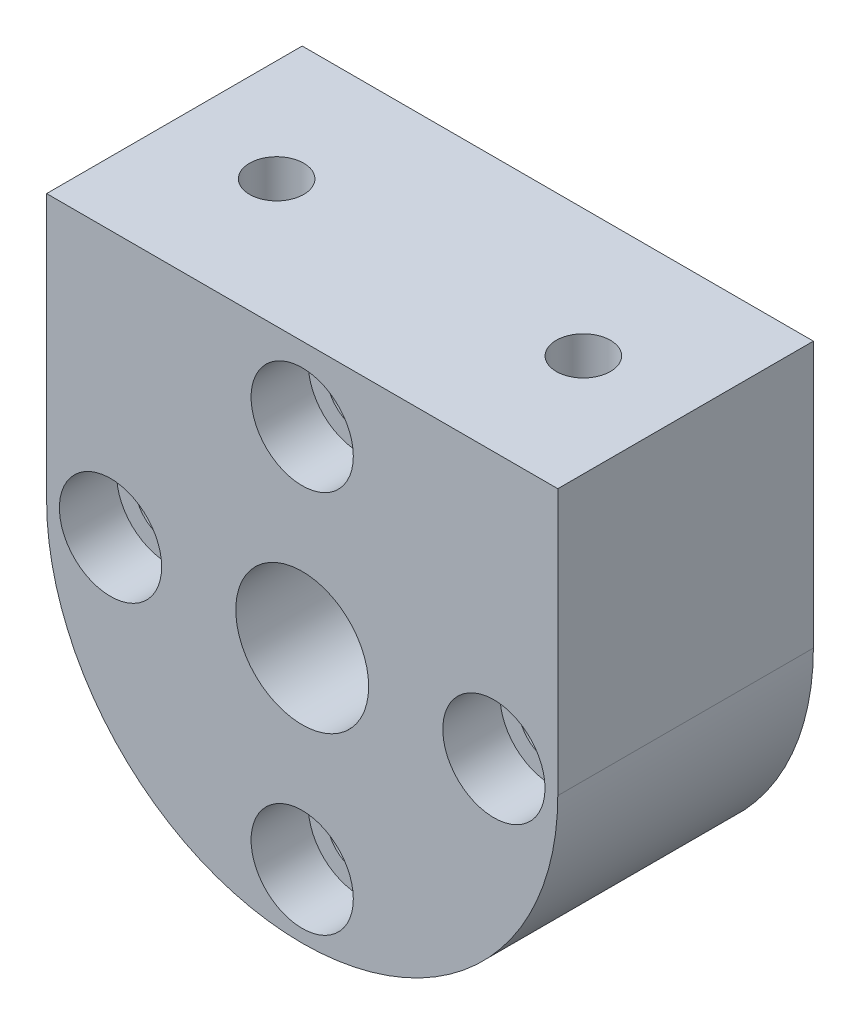
SolidWorks part; units mm, degrees
ref_plane "Front Plane" through (0, 0, 0) normal (0, 0, 1) x (1, 0, 0)
ref_plane "Top Plane" through (0, 0, 0) normal (0, 1, 0) x (1, 0, 0)
ref_plane "Right Plane" through (0, 0, 0) normal (1, 0, 0) x (0, 0, -1)
sketch "Sketch1" plane through (0, 0, 0) normal (0, 0, 1) x (1, 0, 0)
  line L3 (-12.7, 0) -> (-12.7, 13.208)
  line L4 (-12.7, 13.208) -> (12.7, 13.208)
  line L5 (12.7, 0) -> (12.7, 13.208)
  arc A0 (-12.7, 0) -> (12.7, 0) centre (0, 0) ccw
  point P5 (0, 0)
  dimension "D1" = 25.4
  dimension "D2" = 13.208
extrude "Boss-Extrude1" add sketch "Sketch1" along normal blind 12.7
sketch "Sketch2" plane through (0, 0, 12.7) normal (0, 0, 1) x (1, 0, 0)
  circle A0 centre (0, 0) radius 3.302
  dimension "D1" = 6.604
extrude "Cut-Extrude1" cut sketch "Sketch2" against normal blind 12.7
hole_wizard "CBORE for #4 Socket Head Cap Screw1" positions "Sketch3" profile "Sketch5" counterbore size "#4" standard "ANSI Inch" end condition through all
sketch "Sketch3" plane through (0, 0, 12.7) normal (0, 0, 1) x (1, 0, 0)
  circle A0 centre (0, 0) radius 9.525 construction
  point P5 (0, 9.525)
  point P7 (9.525, 0)
  point P9 (0, -9.525)
  point P11 (-9.525, 0)
  dimension "D1" = 19.05
sketch "Sketch5" plane through (-9.525, 0, 12.7) normal (1, 0, 0) x (0, -1, 0)
  line L0 (0, 0) -> (0, 12.7)
  line L1 (0, 12.7) -> (1.6319, 12.7)
  line L3 (1.6319, 12.7) -> (1.632, 2.8448)
  line L4 (1.632, 2.8448) -> (2.54, 2.8448)
  line L5 (2.54, 2.8448) -> (2.54, 0)
  line L7 (2.54, 0) -> (0, 0)
  line L11 (0, -6.35) -> (0, 107.95) construction
  dimension "Thru Hole Dia." = 3.2639
  dimension "Thru Hole Depth" = 12.7
  dimension "C'Bore Dia." = 5.08
  dimension "C'Bore Depth" = 2.8448
sketch "Sketch9" plane through (0, 13.208, 0) normal (0, 1, 0) x (1, 0, 0)
  line L0 (0, 0) -> (0, -12.7) construction
  line L1 (12.7, -12.7) -> (-12.7, -12.7) construction
  line L2 (-7.62, -6.35) -> (7.62, -6.35) construction
  circle A0 centre (-7.62, -6.35) radius 1.3462
  circle A1 centre (7.62, -6.35) radius 1.3462
  point P8 (0, -6.35)
  dimension "D2" = 2.6924
  dimension "D1" = 15.24
extrude "Cut-Extrude3" cut sketch "Sketch9" against normal blind 8.89
thread "Thread1" pitch 0.7937 start angle 0, offset 0, length 0, pitch 0.7937, diameter 2.6924
ref_plane "Plane2" through (-8.9662, 13.208, 6.35) normal (0, 0, 1) x (-1, 0, 0)
sketch "Thread Profile1" plane through (-8.9662, 13.208, 6.35) normal (0, 0, 1) x (-1, 0, 0)
  line L0 (0, 0) -> (0, 0.7937) construction
  line L1 (0, 0) -> (0.4296, 0.248)
  line L2 (0.4296, 0.248) -> (0.4296, 0.3473)
  line L3 (0.4296, 0.3473) -> (0, 0.5953)
  line L4 (0.4296, 0.2977) -> (0, 0.2977) construction
  line L11 (0, 0) -> (0, 0.5953)
  point P2 (0, 0)
  dimension "Pitch" = 0.7937
  dimension "Profile_Angle" = 60
  dimension "Profile_Land" = 0.0992
  dimension "Profile_Height" = 0.4296
thread "Thread2" pitch 0.7937 start angle 0, offset 0, length 0, pitch 0.7937, diameter 2.6924
ref_plane "Plane3" through (6.2738, 13.208, 6.35) normal (0, 0, 1) x (-1, 0, 0)
sketch "Thread Profile2" plane through (6.2738, 13.208, 6.35) normal (0, 0, 1) x (-1, 0, 0)
  line L0 (0, 0) -> (0, 0.7937) construction
  line L1 (0, 0) -> (0.4296, 0.248)
  line L2 (0.4296, 0.248) -> (0.4296, 0.3473)
  line L3 (0.4296, 0.3473) -> (0, 0.5953)
  line L4 (0.4296, 0.2977) -> (0, 0.2977) construction
  line L11 (0, 0) -> (0, 0.5953)
  point P2 (0, 0)
  dimension "Pitch" = 0.7937
  dimension "Profile_Angle" = 60
  dimension "Profile_Land" = 0.0992
  dimension "Profile_Height" = 0.4296
